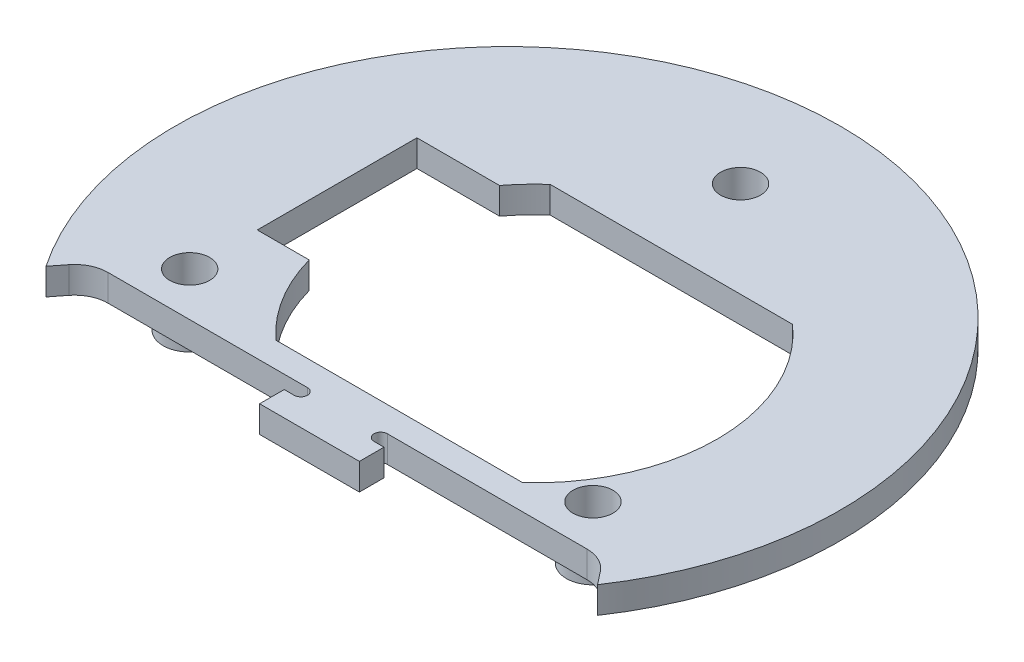
SolidWorks part; units mm, degrees
material "ABS"
ref_plane "Front Plane" through (0, 0, 0) normal (0, 0, 1) x (1, 0, 0)
ref_plane "Top Plane" through (0, 0, 0) normal (0, 1, 0) x (1, 0, 0)
ref_plane "Right Plane" through (0, 0, 0) normal (1, 0, 0) x (0, 0, -1)
sketch "Sketch1" plane through (0, 0, 0) normal (0, 1, 0) x (1, 0, 0)
  circle A0 centre (0, 0) radius 50
  dimension "D1" = 100
extrude "Boss-Extrude1" add sketch "Sketch1" along normal blind 4
sketch "Sketch2" plane through (0, 0, 0) normal (0, 1, 0) x (1, 0, 0)
  line L0 (0, -2.2) -> (0, 2.2) construction
  circle A0 centre (0, 35) radius 3
  dimension "D1" = 6
  dimension "D2" = 38
extrude "Cut-Extrude1" cut sketch "Sketch2" along normal through all both and the other way through all
pattern_circular "CirPattern1" count 3 over 360 about axis through (0, 0, 0) along (0, 1, 0) of "Cut-Extrude1"
sketch "Sketch3" plane through (0, 0, 0) normal (0, -1, 0) x (1, 0, 0)
  circle A0 centre (0, -35) radius 4
  dimension "D1" = 8
extrude "Boss-Extrude3" add sketch "Sketch3" along normal blind 4
sketch "Sketch4" plane through (0, 0, 0) normal (0, -1, 0) x (1, 0, 0)
  circle A0 centre (0, -35) radius 3
  dimension "D1" = 6
extrude "Cut-Extrude2" cut sketch "Sketch4" along normal through all
pattern_circular "CirPattern2" count 3 over 360 about axis through (0, 0, 0) along (0, 1, 0) of "Boss-Extrude3", "Cut-Extrude2"
sketch "Sketch5" plane through (0, 0, 0) normal (0, 1, 0) x (1, 0, 0)
  line L0 (-36, -24.1) -> (-6, -24.1)
  line L1 (-39.9351, -26.0154) -> (-41.4553, -27.9546)
  line L2 (0, -4.4) -> (0, 4.4) construction
  line L3 (-6, -26.1) -> (-7.5, -26.1)
  line L4 (-7.5, -26.1) -> (-7.5, -29.8)
  line L5 (-7.5, -29.8) -> (7.5, -29.8)
  line L6 (7.5, -26.1) -> (7.5, -29.8)
  line L7 (6, -26.1) -> (7.5, -26.1)
  line L8 (39.9351, -26.0154) -> (41.4553, -27.9546)
  line L9 (36, -24.1) -> (6, -24.1)
  arc A0 (-36, -24.1) -> (-39.9351, -26.0154) centre (-36, -29.1) ccw
  arc A1 (-41.4553, -27.9546) -> (41.4553, -27.9546) centre (0, 0) ccw
  circle A2 centre (0, 0) radius 50 construction
  arc A3 (-6, -26.1) -> (-6, -24.1) centre (-6, -25.1) ccw
  arc A4 (6, -26.1) -> (6, -24.1) centre (6, -25.1) cw
  arc A5 (36, -24.1) -> (39.9351, -26.0154) centre (36, -29.1) cw
  point P25 (0, -29.8)
  dimension "D1" = 36
  dimension "D5" = 5
  dimension "D6" = 6
  dimension "D3" = 2
  dimension "D4" = 0
  dimension "D7" = 1.5
  dimension "D8" = 3.7
extrude "Cut-Extrude4" cut sketch "Sketch5" along normal through all
sketch "Sketch6" plane through (0, 4, 0) normal (0, 1, 0) x (1, 0, 0)
  line L0 (-30.3, -7.35) -> (-30.3, 16.65)
  line L1 (-30.3, -7.35) -> (-22.4996, -7.35)
  line L2 (-6, -24.1) -> (-36, -24.1) construction
  line L3 (-30.3, 16.65) -> (-17.8867, 16.65)
  line L4 (-14.2178, 20.6) -> (22.2178, 20.6)
  line L6 (22.5515, -20.3) -> (-14.5515, -20.3)
  line L7 (36, -24.1) -> (6, -24.1) construction
  arc A0 (-14.2178, 20.6) -> (-17.8867, 16.65) centre (4, 0) ccw
  arc A1 (22.5515, -20.3) -> (22.2178, 20.6) centre (4, 0) ccw
  arc A2 (-22.4996, -7.35) -> (-14.5515, -20.3) centre (4, 0) ccw
  arc A3 (41.4553, -27.9546) -> (-41.4553, -27.9546) centre (0, 0) ccw construction
  dimension "D7" = 55
  dimension "D1" = 24
  dimension "D2" = 19.7
  dimension "D3" = 16.75
  dimension "D9" = 3.8
  dimension "D5" = 40.9
  dimension "D8" = 46
  dimension "D10" = 0
extrude "Cut-Extrude5" cut sketch "Sketch6" against normal through all
equation "\"D8@Sketch6\"=\"D7@Sketch6\"/2 + 0.0185"
